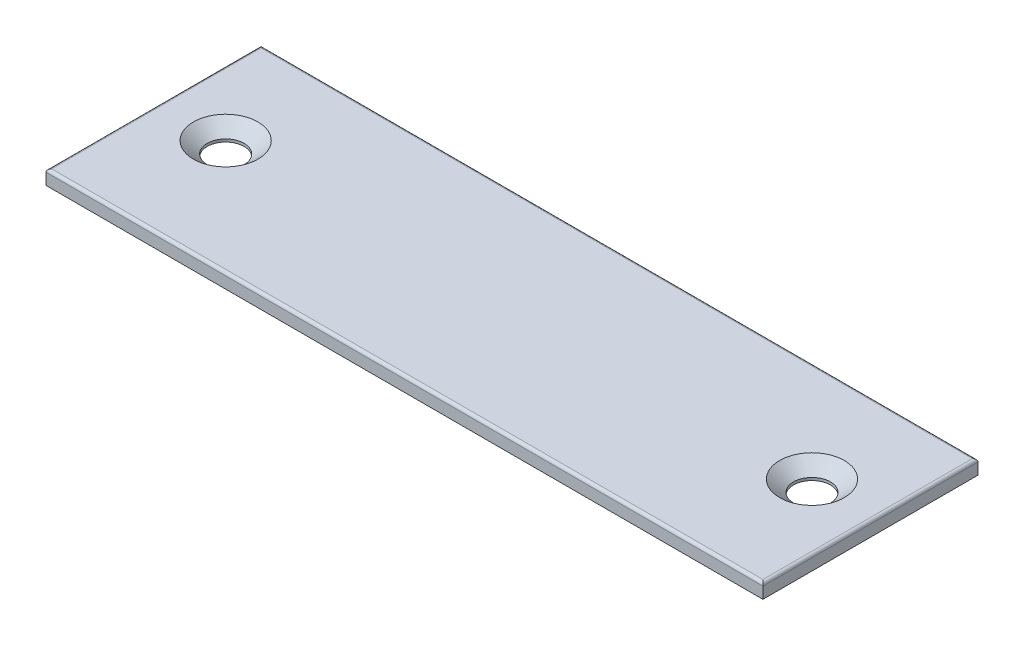
SolidWorks part; units mm, degrees
material "1060 Alloy"
ref_plane "Front Plane" through (0, 0, 0) normal (0, 0, 1) x (1, 0, 0)
ref_plane "Top Plane" through (0, 0, 0) normal (0, 1, 0) x (1, 0, 0)
ref_plane "Right Plane" through (0, 0, 0) normal (1, 0, 0) x (0, 0, -1)
sketch "Sketch1" plane through (0, 0, 0) normal (0, 1, 0) x (1, 0, 0)
  line L1 (-51.3662, 4.15) -> (-51.3662, 64.6221)
  line L2 (51.3662, 4.15) -> (51.3662, 64.6221)
  line L3 (-51.3662, 4.15) -> (-19.05, 4.15)
  line L4 (0, 0) -> (101.6, 0) construction
  line L5 (0, 0) -> (-101.6, 0) construction
  line L9 (0, 9.525) -> (0, 14.2875) construction
  line L10 (-2.3813, 14.2875) -> (2.3813, 14.2875) construction
  line L11 (-2.3813, 14.2875) -> (-2.3813, 9.2225) construction
  line L12 (2.3813, 14.2875) -> (2.3813, 9.2225) construction
  line L18 (0, 9.525) -> (19.05, 9.525) construction
  line L24 (-19.05, 14.2875) -> (-19.05, -14.224) construction
  line L25 (-19.05, -14.224) -> (19.05, -14.224) construction
  line L26 (19.05, 14.2875) -> (19.05, -14.224) construction
  line L27 (0, 9.525) -> (-19.05, 9.525) construction
  line L30 (19.05, 14.2875) -> (-19.05, 14.2875) construction
  line L31 (19.05, 4.15) -> (51.3662, 4.15)
  line L33 (19.05, 14.2875) -> (19.05, 4.15)
  line L35 (-19.05, 14.2875) -> (-19.05, 4.15)
  line L36 (19.05, 18.374) -> (-19.05, 18.374)
  line L37 (19.05, 18.374) -> (19.05, 14.2875)
  line L38 (-19.05, 18.374) -> (-19.05, 14.2875)
  line L39 (0, 30.8499) -> (0, 0) construction
  line L40 (31.75, 11.7999) -> (-31.75, 11.7999)
  line L41 (31.75, 11.7999) -> (31.75, 30.8499)
  line L42 (31.75, 30.8499) -> (-31.75, 30.8499)
  line L43 (-31.75, 11.7999) -> (-31.75, 30.8499)
  circle A0 centre (0, 0) radius 101.6 construction
  circle A1 centre (0, 0) radius 88.9 construction
  circle A2 centre (0, 0) radius 82.55 construction
  arc A3 (-51.3662, 64.6221) -> (51.3662, 64.6221) centre (0, 0) cw
  arc A4 (-51.3662, -64.6221) -> (51.3662, -64.6221) centre (0, 0) ccw construction
  circle A5 centre (0, 0) radius 9.525 construction
  point P8 (0, 0)
  point P22 (0, 14.2875)
  dimension "D1" = 165.1
  dimension "D2" = 203.2
  dimension "D3" = 6.35
  dimension "D4" = 19.05
  dimension "D10" = 110.8821
  dimension "D5" = 4.7625
  dimension "D6" = 4.7625
  dimension "D7" = 38.1
  dimension "D8" = 38.1
  dimension "D9" = 14.224
  dimension "D11" = 4.15
  dimension "D12" = 14.224
  dimension "D14" = 19.05
  dimension "D15" = 63.5
ref_point "Point1"
extrude "Boss-Extrude1" add sketch "Sketch1" along normal blind 1.27 contours L42 L43 L40 L41
hole_wizard "CSK for #4 Flat Head Machine Screw (100)2" positions "Sketch14" profile "Sketch15" countersink size "#4" standard "ANSI Inch" end condition up to next
sketch "Sketch14" plane through (0, 1.27, 0) normal (0, 1, 0) x (1, 0, 0)
  line L6 (19.05, 4.15) -> (51.3662, 4.15) construction
  line L7 (51.3662, 4.15) -> (51.3662, 64.6221) construction
  line L8 (-51.3662, 4.15) -> (-19.05, 4.15) construction
  line L9 (-51.3662, 4.15) -> (-51.3662, 64.6221) construction
  point P0 (-25.9662, 21.93)
  point P2 (25.9662, 21.93)
  dimension "D1" = 17.78
  dimension "D2" = 25.4
  dimension "D3" = 17.78
  dimension "D4" = 25.4
sketch "Sketch15" plane through (-25.9662, 1.27, -21.93) normal (1, 0, 0) x (0, 0, 1)
  line L0 (0, 0) -> (0, 1.27)
  line L1 (0, 1.27) -> (1.6319, 1.27)
  line L2 (1.6319, 1.27) -> (1.632, 1.0284)
  line L3 (1.632, 1.0284) -> (2.8575, 0)
  line L5 (2.8575, 0) -> (0, 0)
  line L6 (-1.632, 1.0284) -> (-2.8575, 0) construction
  line L11 (0, -6.35) -> (0, 107.95) construction
  dimension "Thru Hole Dia." = 3.2639
  dimension "Thru Hole Depth" = 1.27
  dimension "Near C'Sink Dia." = 5.715
  dimension "Near C'Sink Angle" = 100
fillet "Fillet2" radius 0.254 4 edges at (-31.75, 1.27, -21.3249) (31.75, 1.27, -21.3249) (0, 1.27, -30.8499) (0, 1.27, -11.7999)
